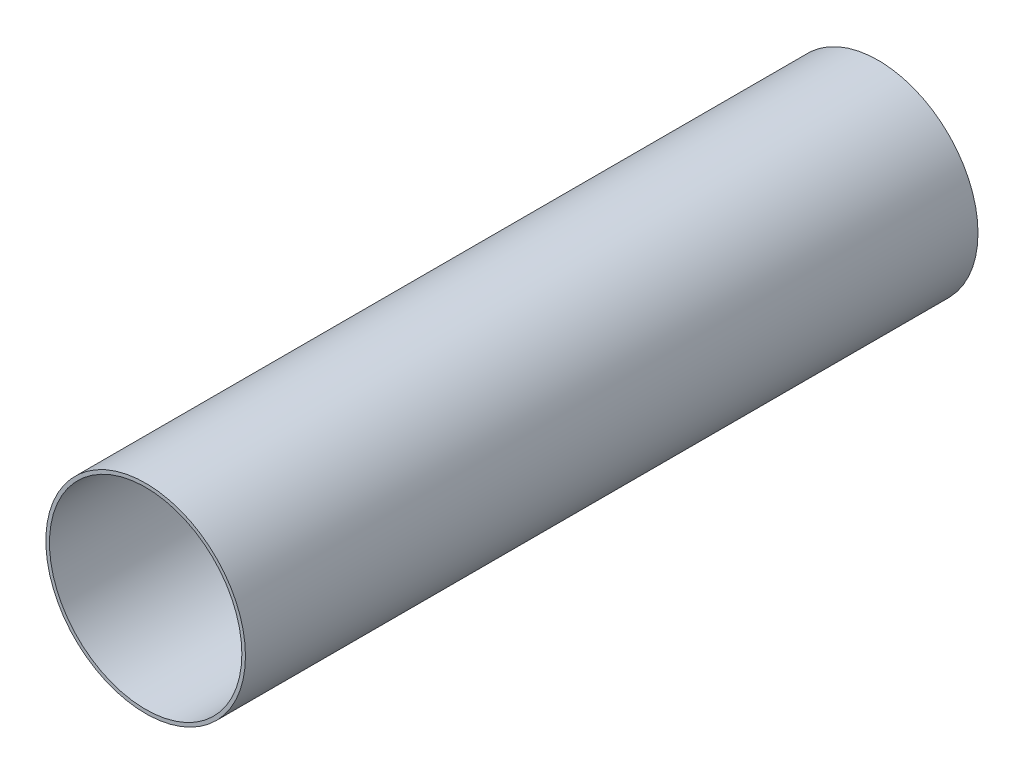
SolidWorks part; units mm, degrees
ref_plane "Front Plane" through (0, 0, 0) normal (0, 0, 1) x (1, 0, 0)
ref_plane "Top Plane" through (0, 0, 0) normal (0, 1, 0) x (1, 0, 0)
ref_plane "Right Plane" through (0, 0, 0) normal (1, 0, 0) x (0, 0, -1)
sketch "Sketch1" plane through (0, 0, 0) normal (0, 0, 1) x (1, 0, 0)
  circle A0 centre (0, 0) radius 20.7645
  dimension "D1" = 41.529
extrude "Extrude-Thin1" add sketch "Sketch1" along normal blind 152.4 thin thin type one direction reverse wall 0.75
